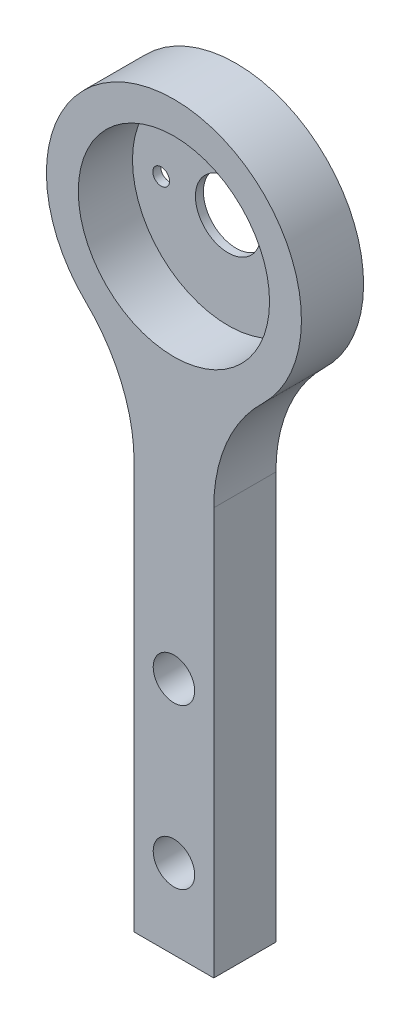
SolidWorks part; units mm, degrees
material "Nylon 101"
ref_plane "Front Plane" through (0, 0, 0) normal (0, 0, 1) x (1, 0, 0)
ref_plane "Top Plane" through (0, 0, 0) normal (0, 1, 0) x (1, 0, 0)
ref_plane "Right Plane" through (0, 0, 0) normal (1, 0, 0) x (0, 0, -1)
sketch "Sketch1" plane through (0, 0, 0) normal (0, 0, 1) x (1, 0, 0)
  line L2 (-2.5, -12.9518) -> (-2.5, -38.5)
  line L3 (-2.5, -38.5) -> (2.5, -38.5)
  line L4 (2.5, -12.9518) -> (2.5, -38.5)
  circle A0 centre (0, 0) radius 6
  arc A1 (5.5556, -5.7564) -> (-5.5556, -5.7564) centre (0, 0) ccw
  arc A2 (5.5556, -5.7564) -> (2.5, -12.9518) centre (12.5, -12.9518) ccw
  arc A3 (-5.5556, -5.7564) -> (-2.5, -12.9518) centre (-12.5, -12.9518) cw
  point P3 (0, -38.5)
  dimension "D1" = 12
  dimension "D2" = 2
  dimension "D5" = 10
  dimension "D4" = 38.5
  dimension "D3" = 5
extrude "Boss-Extrude1" add sketch "Sketch1" along normal blind 3.9
sketch "Sketch4" plane through (0, 0, 0) normal (0, 0, 1) x (1, 0, 0)
  line L0 (4.2, 0) -> (-4.2, 0) construction
  circle A0 centre (0, 0) radius 8
  circle A1 centre (0, 0) radius 6
  circle A2 centre (0, 0) radius 6 construction
  arc A3 (5.5556, -5.7564) -> (-5.5556, -5.7564) centre (0, 0) ccw construction
  circle A4 centre (4.2, 0) radius 0.525
  circle A5 centre (-4.2, 0) radius 0.525
  point P16 (0, 0)
  dimension "D1" = 1.05
  dimension "D2" = 8.4
sketch "Sketch5" plane through (0, 0, 0) normal (0, 0, -1) x (-1, 0, 0)
  circle A0 centre (0, 0) radius 2.05
  circle A1 centre (4.2, 0) radius 0.525
  circle A2 centre (4.2, 0) radius 0.525
  circle A3 centre (-4.2, 0) radius 0.525
  circle A4 centre (-4.2, 0) radius 0.525
  circle A7 centre (0, 0) radius 8
  circle A8 centre (0, 0) radius 8
  dimension "D3" = 4.1
  dimension "D1" = 0
  dimension "D2" = 0
  dimension "D4" = 0
extrude "Boss-Extrude3" add sketch "Sketch5" against normal blind 0.5
hole_wizard "CSK for M2 Flat Head Machine Screw1" positions "Sketch6" profile "Sketch7" countersink size "M2" standard "ANSI Metric" end condition through all
sketch "Sketch6" plane through (0, 0, 0) normal (0, 0, -1) x (-1, 0, 0)
  circle A2 centre (0, -23.5) radius 0.8 construction
  circle A3 centre (0, -33.5) radius 0.8 construction
  point P0 (0, -33.5)
  point P2 (0, -23.5)
sketch "Sketch7" plane through (0, -33.5, 0) normal (1, 0, 0) x (0, 1, 0)
  line L0 (0, 0) -> (0, 3.9)
  line L1 (0, 3.9) -> (1.3, 3.9)
  line L2 (1.3, 3.9) -> (1.3, 0.9)
  line L3 (1.3, 0.9) -> (2.2, 0)
  line L5 (2.2, 0) -> (0, 0)
  line L6 (-1.3, 0.9) -> (-2.2, 0) construction
  line L11 (0, -6.35) -> (0, 107.95) construction
  dimension "Thru Hole Dia." = 2.6
  dimension "Thru Hole Depth" = 3.9
  dimension "Near C'Sink Dia." = 4.4
  dimension "Near C'Sink Angle" = 90
